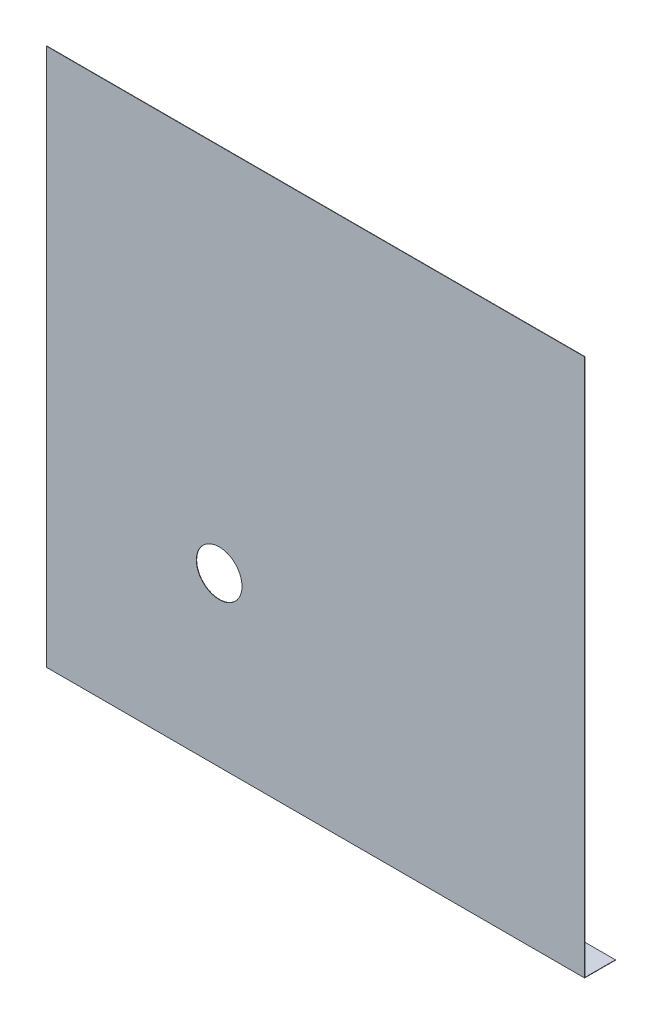
SolidWorks part; units mm, degrees
ref_plane "Front Plane" through (0, 0, 0) normal (0, 0, 1) x (1, 0, 0)
ref_plane "Top Plane" through (0, 0, 0) normal (0, 1, 0) x (1, 0, 0)
ref_plane "Right Plane" through (0, 0, 0) normal (1, 0, 0) x (0, 0, -1)
sketch "Sketch2" plane through (0, 0, 0) normal (1, 0, 0) x (0, 0, -1)
  line L0 (0, -638.845) -> (0, 591.1513) construction
  line L1 (-1149.67, 0) -> (1199.874, 0) construction
  line L2 (0, 530) -> (0.35, 530)
  line L3 (0.35, 530) -> (0.35, 0.35)
  line L4 (0.35, 0.35) -> (30.35, 0.35)
  line L5 (30.35, 0.35) -> (30.35, 0)
  line L6 (30.35, 0) -> (0, 0)
  line L7 (0, 0) -> (0, 530)
  dimension "D1" = 530
  dimension "D2" = 30
  dimension "D3" = 0.35
  dimension "D4" = 0.35
extrude "Boss-Extrude1" add sketch "Sketch2" along normal blind 530
sketch "Sketch3" plane through (0, 0, -0.35) normal (0, 0, -1) x (-1, 0, 0)
  line L0 (-530, 0.35) -> (-530, 530) construction
  line L1 (-530, 0.35) -> (0, 0.35) construction
  circle A0 centre (-170, 165.35) radius 22.5
  dimension "D2" = 165
  dimension "D3" = 45
  dimension "D1" = 360
extrude "Cut-Extrude1" cut sketch "Sketch3" against normal blind 530
